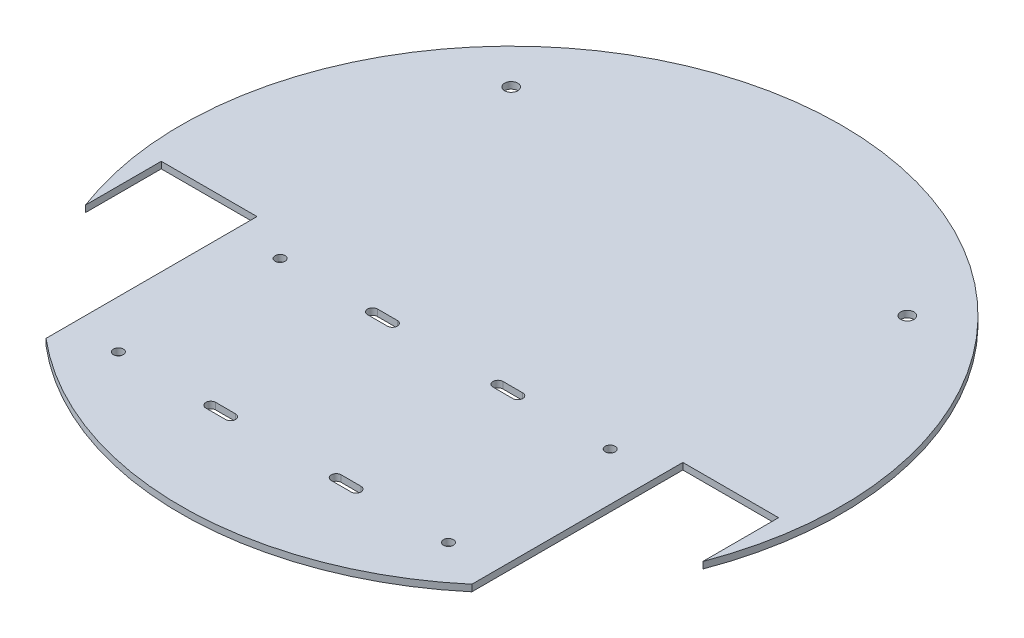
SolidWorks part; units mm, degrees
ref_plane "Front Plane" through (0, 0, 0) normal (0, 0, 1) x (1, 0, 0)
ref_plane "Top Plane" through (0, 0, 0) normal (0, 1, 0) x (1, 0, 0)
ref_plane "Right Plane" through (0, 0, 0) normal (1, 0, 0) x (0, 0, -1)
sketch "Sketch1" plane through (0, 0, 0) normal (0, 1, 0) x (1, 0, 0)
  line L0 (0, 107.5512) -> (0, -106.9432) construction
  line L1 (-159.5954, 0) -> (140.6967, 0) construction
  line L2 (-50, 39.3685) -> (-50, -79.3685) construction
  line L3 (-77.1985, -44.5) -> (15.3752, -44.5) construction
  line L4 (-34.5, -1.9111) -> (-34.5, -79.3685) construction
  line L5 (-16, -20) -> (-22, -20) construction
  line L6 (-16, -21.5) -> (-22, -21.5)
  line L7 (-16, -18.5) -> (-22, -18.5)
  line L8 (-16, -69) -> (-22, -69) construction
  line L9 (-16, -67.5) -> (-22, -67.5)
  line L10 (-16, -70.5) -> (-22, -70.5)
  line L11 (16, -20) -> (22, -20) construction
  line L12 (16, -21.5) -> (22, -21.5)
  line L13 (16, -18.5) -> (22, -18.5)
  line L14 (16, -69) -> (22, -69) construction
  line L15 (16, -67.5) -> (22, -67.5)
  line L16 (16, -70.5) -> (22, -70.5)
  line L17 (-64.5, 38.8079) -> (-64.5, -103.4684) construction
  line L18 (-93.5, 38.8079) -> (-93.5, -35.4648) construction
  line L19 (-93.5, -12.5) -> (-64.5, -12.5)
  line L20 (-64.5, -12.5) -> (-64.5, -76.5)
  line L21 (-93.5, -12.5) -> (-93.5, -35.4648)
  line L23 (93.5, -12.5) -> (64.5, -12.5)
  line L24 (64.5, -12.5) -> (64.5, -76.5)
  line L26 (93.5, -12.5) -> (93.5, -35.4648)
  arc A0 (-64.5, -76.4183) -> (64.5, -76.4183) centre (0, 0) ccw
  circle A1 centre (-50, -20) radius 1.5
  arc A2 (-16, -67.5) -> (-16, -70.5) centre (-16, -69) cw
  arc A3 (-22, -70.5) -> (-22, -67.5) centre (-22, -69) cw
  circle A4 centre (-50, -69) radius 1.5
  arc A5 (-16, -21.5) -> (-16, -18.5) centre (-16, -20) ccw
  arc A6 (-22, -18.5) -> (-22, -21.5) centre (-22, -20) ccw
  arc A7 (16, -21.5) -> (16, -18.5) centre (16, -20) cw
  arc A8 (22, -18.5) -> (22, -21.5) centre (22, -20) cw
  arc A9 (16, -67.5) -> (16, -70.5) centre (16, -69) ccw
  arc A10 (22, -70.5) -> (22, -67.5) centre (22, -69) ccw
  circle A11 centre (50, -69) radius 1.5
  circle A12 centre (50, -20) radius 1.5
  arc A13 (93.5, -35.4648) -> (-93.5, -35.4648) centre (0, 0) ccw
  circle A14 centre (-60, 60) radius 2
  circle A15 centre (60, 60) radius 2
  point P9 (-19, -69)
  point P23 (-19, -20)
  point P33 (19, -20)
  point P40 (19, -69)
  point P58 (-64.5, -44.5)
  point P59 (-93.5, -44.5)
  dimension "D1" = 200
  dimension "D6" = 3
  dimension "D4" = 29
  dimension "D13" = 4
  dimension "D2" = 6
  dimension "D3" = 3
  dimension "D5" = 31
  dimension "D7" = 14.5
  dimension "D8" = 32
  dimension "D9" = 50
  dimension "D10" = 44.5
  dimension "D11" = 60
  dimension "D12" = 60
extrude "Boss-Extrude1" add sketch "Sketch1" along normal blind 2 contours L26 A13 L21 L19 L20 A0 L24 L23 A12 A11 A10 L16 A9 L15 A6 L7 A5 L6 L10 A3 L9 A2 A1 A4 L13 A8 L12 A7
